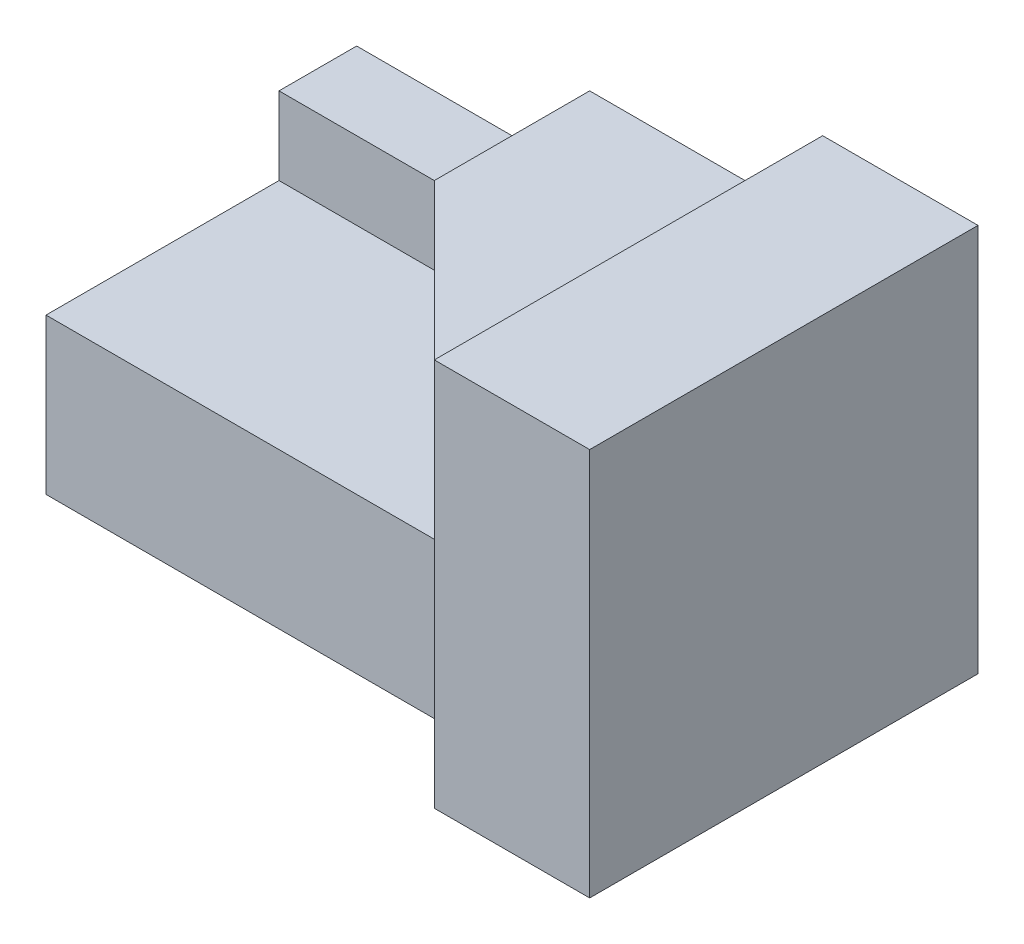
SolidWorks part; units mm, degrees
ref_plane "Front Plane" through (0, 0, 0) normal (0, 0, 1) x (1, 0, 0)
ref_plane "Top Plane" through (0, 0, 0) normal (0, 1, 0) x (1, 0, 0)
ref_plane "Right Plane" through (0, 0, 0) normal (1, 0, 0) x (0, 0, -1)
sketch "Sketch1" plane through (0, 0, 0) normal (0, 0, 1) x (1, 0, 0)
  line L1 (0, 0) -> (80, 0)
  line L2 (0, 0) -> (0, 50)
  line L3 (0, 50) -> (80, 50)
  line L4 (80, 0) -> (80, 50)
  dimension "D1" = 80
  dimension "D2" = 50
extrude "Boss-Extrude2" add sketch "Sketch1" against normal blind 50
sketch "Sketch2" plane through (0, 0, 0) normal (0, 0, 1) x (1, 0, 0)
  line L1 (0, 50) -> (60, 50)
  line L2 (0, 50) -> (0, 40)
  line L3 (0, 40) -> (60, 40)
  line L4 (60, 50) -> (60, 40)
  dimension "D1" = 10
  dimension "D2" = 20
extrude "Cut-Extrude1" cut sketch "Sketch2" against normal blind 50
sketch "Sketch3" plane through (0, 0, 0) normal (0, 0, 1) x (1, 0, 0)
  line L1 (0, 40) -> (30, 40)
  line L2 (0, 40) -> (0, 30)
  line L3 (0, 30) -> (30, 30)
  line L4 (30, 40) -> (30, 30)
  dimension "D1" = 30
  dimension "D2" = 10
extrude "Cut-Extrude2" cut sketch "Sketch3" against normal blind 50
sketch "Sketch4" plane through (0, 0, 0) normal (0, -1, 0) x (1, 0, 0)
  line L0 (0, 0) -> (0, -10)
  line L1 (0, -10) -> (50, -10)
  line L2 (50, -10) -> (60, 0)
  line L3 (0, 0) -> (80, 0) construction
  line L4 (60, 0) -> (0, 0)
  line L5 (60, 0) -> (0, 0)
  line M1 (80, 0) -> (0, 0)
  line M2 (0, 0) -> (0, -50)
  dimension "D1" = 20
  dimension "D2" = 10
  dimension "D3" = 10
extrude "Cut-Extrude3" cut sketch "Sketch4" against normal blind 50 contours L1 L2 M1 M2
sketch "Sketch5" plane through (0, 40, 0) normal (0, 1, 0) x (1, 0, 0)
  line L0 (30, 50) -> (60, 50)
  line L1 (60, 50) -> (60, 0)
  line L2 (60, 0) -> (30, 30)
  line L3 (30, 50) -> (30, 10) construction
  line L4 (30, 30) -> (30, 50)
  line L5 (30, 30) -> (30, 10)
  line L6 (30, 10) -> (50, 10)
  line M1 (30, 50) -> (30, 10)
  line M2 (30, 10) -> (50, 10)
extrude "Cut-Extrude4" cut sketch "Sketch5" against normal blind 20 contours L2 M2 M1
sketch "Sketch6" plane through (0, 30, 0) normal (0, 1, 0) x (1, 0, 0)
  line L0 (0, 10) -> (50, 10)
  line L1 (50, 10) -> (20, 40)
  line L2 (20, 40) -> (0, 40)
  line L3 (0, 50) -> (0, 10) construction
  line L4 (0, 40) -> (0, 10)
  dimension "D1" = 10
  dimension "D2" = 20
extrude "Cut-Extrude5" cut sketch "Sketch6" against normal blind 10
